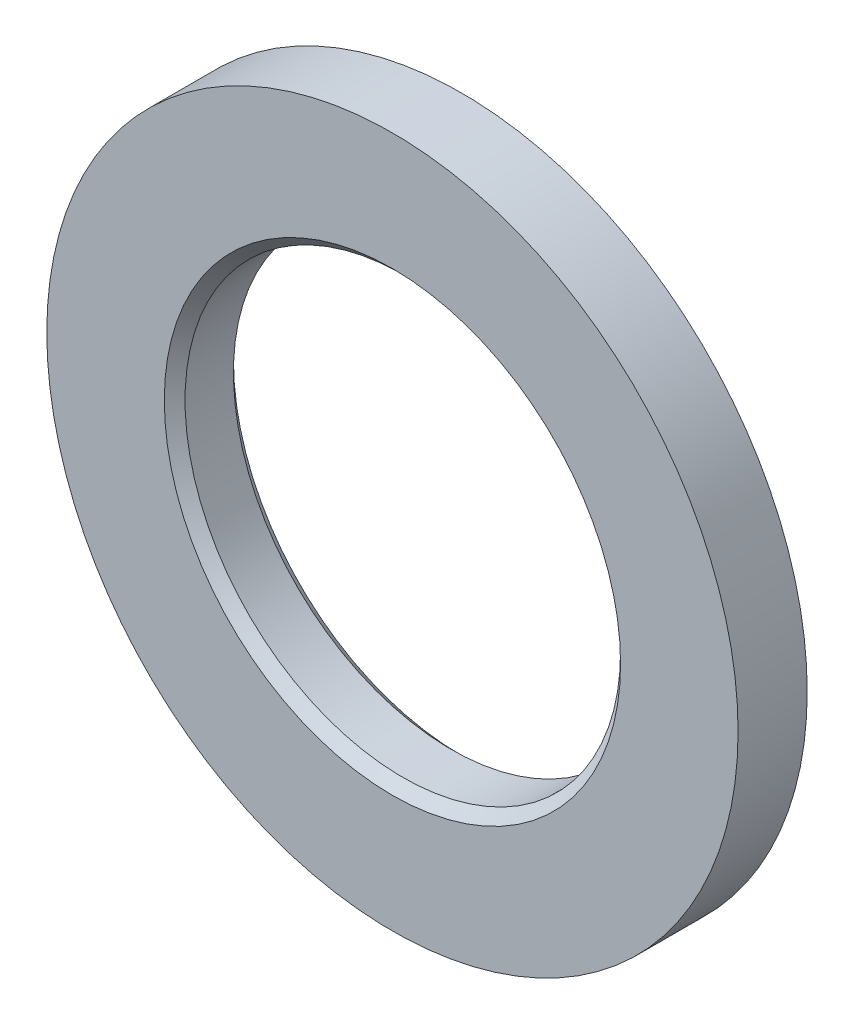
SolidWorks part; units mm, degrees
ref_plane "Front" through (0, 0, 0) normal (0, 0, 1) x (1, 0, 0)
ref_plane "Top" through (0, 0, 0) normal (0, 1, 0) x (1, 0, 0)
ref_plane "Right" through (0, 0, 0) normal (1, 0, 0) x (0, 0, -1)
sketch "Guard base" plane through (0, 0, 0) normal (0, 0, 1) x (1, 0, 0)
  circle A0 centre (0, 0) radius 25
  dimension "D1" = 50
extrude "Guard" add sketch "Guard base" along normal blind 5
sketch "Axle hole base" plane through (0, 0, 5) normal (0, 0, 1) x (1, 0, 0)
  circle A0 centre (0, 0) radius 15.75
  dimension "D1" = 31.5
extrude "Axle hole" cut sketch "Axle hole base" against normal through all
ref_axis "Center Z" through (0, 0, 0) along (0, 0, -1)
sketch "Mate ring room base" plane through (0, 0, 0) normal (0, 1, 0) x (1, 0, 0)
  line L0 (15.75, -5) -> (16.5, -5)
  line L1 (16.5, -5) -> (15.75, -4.25)
  line L2 (15.75, -4.25) -> (15.75, -5)
  line L5 (15.75, 0) -> (16.5, 0)
  line L6 (15.75, 0) -> (15.75, -0.75)
  line L7 (15.75, -0.75) -> (16.5, 0)
  dimension "D1" = 0.75
revolve "Mate ring room" cut sketch "Mate ring room base" angle 360 about axis through (0, 0, 0) along (0, 0, -1)
equation "\"mate_room\"= 0.25"
equation "\"removal_room\"= 0.75"
equation "\"large_inner_axle_diameter\"=20"
equation "\"D1@Axle hole base\"=\"32_92_spool_inner_diameter\"-\"spool_inner_diameter_room\"+\"mate_room\"*2"
equation "\"guard_thickness\"=5"
equation "\"spool_inner_diameter_room\"=1"
equation "\"32_92_coupling_tooth_height\"=13"
equation "\"32_92_coupling_tooth_thickness_total\"=4"
equation "\"32_92_coupling_tooth_protrusion\"=1"
equation "\"32_92_coupling_tooth_depth\"=8"
equation "\"32_92_coupling_tooth_base_thickness\"=5.5"
equation "\"D1@Guard\"=\"guard_thickness\""
equation "\"32_92_guard_diameter\"=50"
equation "\"D1@Guard base\"=\"32_92_guard_diameter\""
equation "\"32_92_coupling_tooth_head_height\"=4"
equation "\"32_92_spool_inner_diameter\"=32"
equation "\"32_92_spool_thickness\"=92"
equation "\"D1@Mate ring room base\" = \"removal_room\""
